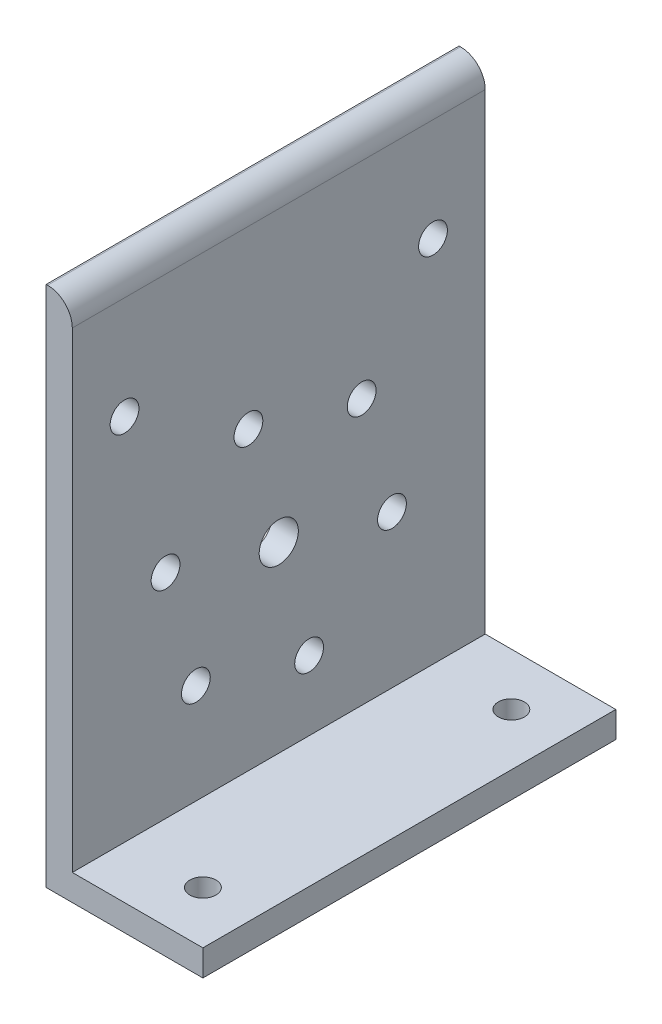
SolidWorks part; units mm, degrees
ref_plane "Front Plane" through (0, 0, 0) normal (0, 0, 1) x (1, 0, 0)
ref_plane "Top Plane" through (0, 0, 0) normal (0, 1, 0) x (1, 0, 0)
ref_plane "Right Plane" through (0, 0, 0) normal (1, 0, 0) x (0, 0, -1)
sketch "Sketch1" plane through (0, 0, 0) normal (0, 0, 1) x (1, 0, 0)
  line L2 (0, 0) -> (0, 127)
  line L3 (0, 127) -> (0.35, 127)
  line L4 (6.35, 37.75) -> (6.35, 121)
  line L6 (0, 0) -> (0, 6.35)
  line L8 (38.1, 0) -> (38.1, 0.35)
  line L9 (6.35, 6.35) -> (6.35, 37.75)
  line L11 (32.1, 6.35) -> (38.1, 6.35)
  line L12 (38.1, 6.35) -> (38.1, 0.35)
  line L13 (38.1, 0) -> (0, 0)
  line L14 (6.35, 6.35) -> (32.1, 6.35)
  arc A1 (0.35, 127) -> (6.35, 121) centre (0.35, 121) cw
  point P10 (38.1, 6.35)
  point P13 (6.35, 127)
  dimension "D1" = 127
  dimension "D2" = 38.1
  dimension "D3" = 6.35
  dimension "D4" = 6.35
extrude "Boss-Extrude1" add sketch "Sketch1" along normal blind 100.4
sketch "Sketch2" plane through (0, 0, 0) normal (-1, 0, 0) x (0, 0, 1)
  line L0 (50.2, 127) -> (50.2, 0)
  line L1 (57.5763, 78.3289) -> (50.2, 50.8)
  line L3 (100.4, 50.8) -> (0, 50.8) construction
  line L4 (100.4, 0) -> (100.4, 127) construction
  line L5 (0, 0) -> (0, 127) construction
  line L6 (100.4, 0) -> (0, 0) construction
  line L7 (100.4, 127) -> (0, 127) construction
  circle A9 centre (50.2, 50.8) radius 4.7625
  circle A17 centre (57.5763, 78.3289) radius 3.5
  circle A25 centre (50.2, 50.8) radius 28.5
  circle A26 centre (77.7289, 58.1763) radius 3.5
  circle A27 centre (70.3525, 30.6475) radius 3.5
  circle A28 centre (42.8237, 23.2711) radius 3.5
  circle A29 centre (22.6711, 43.4237) radius 3.5
  circle A30 centre (30.0475, 70.9525) radius 3.5
  dimension "D1" = 57
  dimension "D2" = 15
  dimension "D4" = 9.525
  dimension "D5" = 6
  dimension "D6" = 7
  dimension "D3" = 50.8
extrude "Cut-Extrude1" cut sketch "Sketch2" against normal through all both and the other way through all
sketch "Sketch3" plane through (0, 6.35, 0) normal (0, 1, 0) x (1, 0, 0)
  line L0 (25.4, -100.4) -> (25.4, 0) construction
  line L4 (6.35, -100.4) -> (38.1, -100.4) construction
  line L5 (6.35, 0) -> (38.1, 0) construction
  line L6 (0, -100.4) -> (0, 0) construction
  circle A0 centre (25.4, -12.7) radius 3.175
  circle A2 centre (25.4, -87.7) radius 3.175
  dimension "D2" = 6.35
  dimension "D3" = 12.7
  dimension "D4" = 12.7
  dimension "D5" = 6.35
  dimension "D1" = 25.4
extrude "Cut-Extrude2" cut sketch "Sketch3" against normal through all
ref_plane "Width Centerline Plane" through (0, 0, 50.2) normal (0, 0, 1) x (1, 0, 0)
sketch "Sketch5" plane through (6.35, 0, 0) normal (1, 0, 0) x (0, 0, -1)
  line L0 (-50.2, 6.35) -> (-50.2, 121) construction
  line L1 (-100.4, 121) -> (0, 121) construction
  line L2 (-100.4, 6.35) -> (0, 6.35) construction
  line L3 (-100.4, 6.35) -> (-100.4, 121) construction
  circle A0 centre (-87.7, 96) radius 3.5
  circle A2 centre (-12.7, 96) radius 3.5
  dimension "D1" = 7
  dimension "D2" = 25
  dimension "D3" = 12.7
extrude "Cut-Extrude4" cut sketch "Sketch5" against normal blind 10
